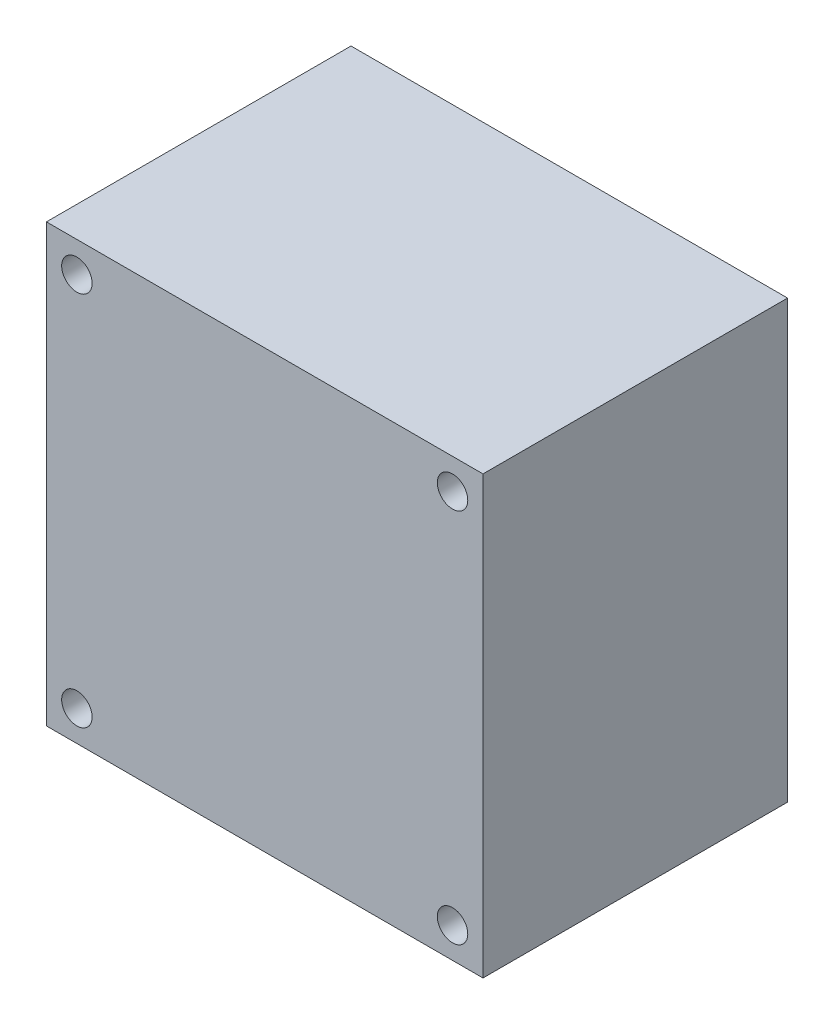
SolidWorks part; units mm, degrees
ref_plane "Plan de face" through (0, 0, 0) normal (0, 0, 1) x (1, 0, 0)
ref_plane "Plan de dessus" through (0, 0, 0) normal (0, 1, 0) x (1, 0, 0)
ref_plane "Plan de droite" through (0, 0, 0) normal (1, 0, 0) x (0, 0, -1)
sketch "Esquisse1" plane through (0, 0, 0) normal (0, 0, 1) x (1, 0, 0)
  line L1 (0, 0) -> (43, 0)
  line L2 (0, 0) -> (0, 43)
  line L3 (0, 43) -> (43, 43)
  line L4 (43, 0) -> (43, 43)
  dimension "D1" = 43
  dimension "D2" = 43
extrude "Boss.-Extru.1" add sketch "Esquisse1" along normal blind 30
sketch "Esquisse2" plane through (0, 0, 30) normal (0, 0, 1) x (1, 0, 0)
  line L0 (43, 43) -> (0, 43) construction
  line L1 (3, 40) -> (40, 40) construction
  line L2 (3, 40) -> (3, 3) construction
  line L3 (3, 3) -> (40, 3) construction
  line L4 (40, 40) -> (40, 3) construction
  line L5 (0, 43) -> (0, 0) construction
  circle A0 centre (3, 40) radius 1.5
  circle A1 centre (40, 40) radius 1.5
  circle A2 centre (40, 3) radius 1.5
  circle A3 centre (3, 3) radius 1.5
  dimension "D5" = 3
  dimension "D6" = 3
  dimension "D7" = 3
  dimension "D8" = 3
  dimension "D1" = 37
  dimension "D2" = 37
  dimension "D3" = 3
  dimension "D4" = 3
extrude "Enlèv. mat.-Extru.1" cut sketch "Esquisse2" against normal through all
